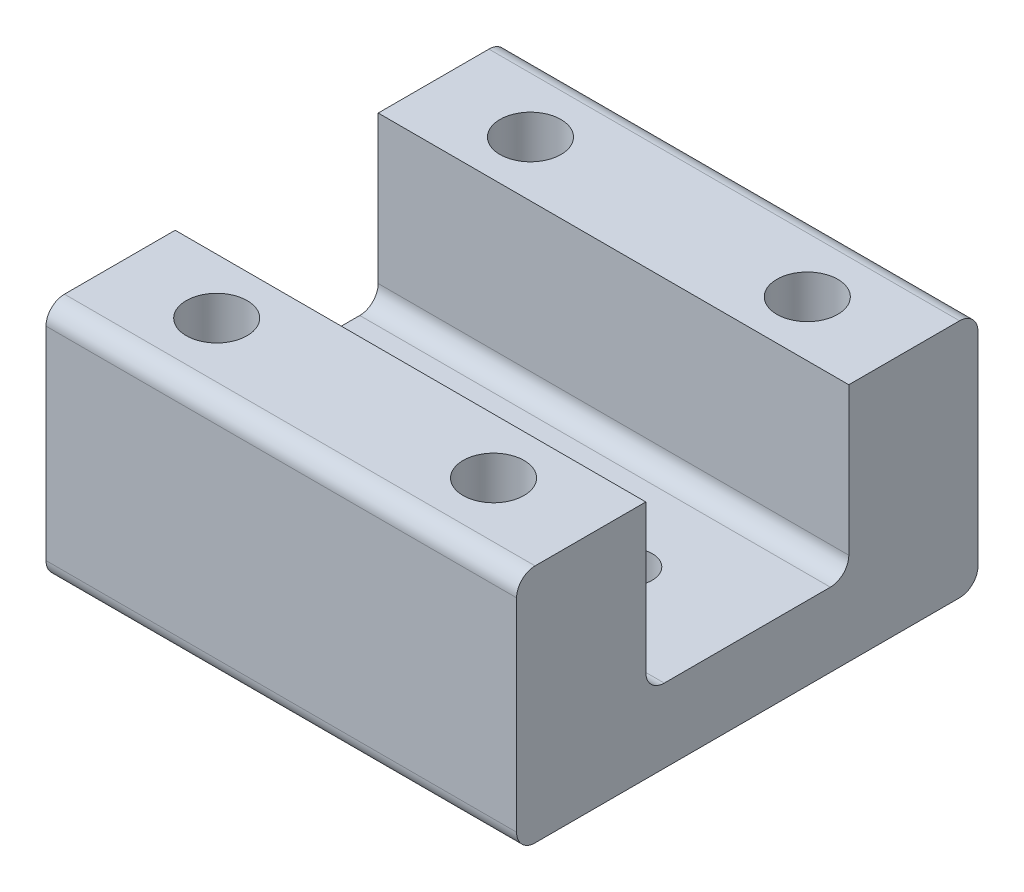
SolidWorks part; units mm, degrees
material "6063-T5"
ref_plane "前视基准面" through (0, 0, 0) normal (0, 0, 1) x (1, 0, 0)
ref_plane "上视基准面" through (0, 0, 0) normal (0, 1, 0) x (1, 0, 0)
ref_plane "右视基准面" through (0, 0, 0) normal (1, 0, 0) x (0, 0, -1)
other "Configuration Table"
sketch "草图1" plane through (0, 0, 0) normal (0, 1, 0) x (1, 0, 0)
  line L1 (-12.75, -12.5) -> (12.75, -12.5)
  line L2 (-12.75, -12.5) -> (-12.75, 12.5)
  line L3 (-12.75, 12.5) -> (12.75, 12.5)
  line L4 (12.75, -12.5) -> (12.75, 12.5)
  line L5 (-12.75, -12.5) -> (12.75, 12.5) construction
  line L6 (-12.75, 12.5) -> (12.75, -12.5) construction
  point P0 (0, 0)
  dimension "D1" = 25.5
  dimension "D2" = 25
extrude "凸台-拉伸1" add sketch "草图1" along normal blind 4
sketch "草图2" plane through (0, 0, 0) normal (0, -1, 0) x (1, 0, 0)
  line L1 (-7.5, 7.5) -> (7.5, 7.5) construction
  line L2 (-7.5, 7.5) -> (-7.5, -7.5) construction
  line L3 (-7.5, -7.5) -> (7.5, -7.5) construction
  line L4 (7.5, 7.5) -> (7.5, -7.5) construction
  line L5 (-7.5, 7.5) -> (7.5, -7.5) construction
  line L6 (-7.5, -7.5) -> (7.5, 7.5) construction
  point P0 (0, 0)
  dimension "D1" = 15
sketch "草图5" plane through (0, 0, 0) normal (0, -1, 0) x (1, 0, 0)
  line L0 (0, 0) -> (50000, 0) construction
  line L1 (12.75, 12.5) -> (12.75, -12.5) construction
  circle A0 centre (6.35, 0) radius 1.525
  circle A1 centre (-6.35, 0) radius 1.525
  dimension "D2" = 3.05
  dimension "D3" = 6.4
  dimension "D1" = 12.7
sketch "草图6" plane through (0, 4, 0) normal (0, 1, 0) x (1, 0, 0)
  line L0 (-12.75, 12.5) -> (-12.75, -12.5) construction
  line L1 (12.75, 12.5) -> (-12.75, 12.5)
  line L2 (12.75, 12.5) -> (12.75, 5.5)
  line L3 (12.75, 5.5) -> (-12.75, 5.5)
  line L4 (-12.75, 12.5) -> (-12.75, 5.5)
  line L5 (0, 0) -> (12.75, 0) construction
  line L6 (12.75, -12.5) -> (-12.75, -12.5)
  line L7 (12.75, -12.5) -> (12.75, -5.5)
  line L8 (12.75, -5.5) -> (-12.75, -5.5)
  line L9 (-12.75, -12.5) -> (-12.75, -5.5)
  line L10 (12.75, -12.5) -> (12.75, 12.5) construction
  dimension "D1" = 7
extrude "凸台-拉伸2" add sketch "草图6" along normal blind 9
sketch "草图7" plane through (0, 0, 0) normal (0, -1, 0) x (1, 0, 0)
  line L0 (-12.75, -12.5) -> (-12.75, 12.5) construction
  line L1 (-7.5, 8.5) -> (7.5, 8.5) construction
  line L2 (-7.5, 8.5) -> (-7.5, -8.5) construction
  line L3 (-7.5, -8.5) -> (7.5, -8.5) construction
  line L4 (7.5, 8.5) -> (7.5, -8.5) construction
  circle A0 centre (7.5, -8.5) radius 2.025
  circle A1 centre (-7.5, 8.5) radius 2.025
  circle A2 centre (7.5, 8.5) radius 2.025
  circle A3 centre (-7.5, -8.5) radius 2.025
  dimension "D1" = 4.05
  dimension "D2" = 15
  dimension "D3" = 8.5
  dimension "D4" = 5.25
  dimension "D5" = 8.5
hole_wizard "M3 螺纹孔1" positions "3D草图3" profile "草图10" tap size "M3" standard "GB" end condition through all
sketch3d "3D草图3"
  point P0 (6.35, 0, 0)
  point P3 (-6.35, 0, 0)
sketch "草图10" plane through (6.35, 0, 0) normal (1, 0, 0) x (0, 0, -1)
  line L0 (0, 0) -> (0, 13)
  line L1 (0, 13) -> (1.25, 13)
  line L2 (1.25, 13) -> (1.25, 0)
  line L5 (1.25, 0) -> (0, 0)
  line L11 (0, -6.35) -> (0, 107.95) construction
  dimension "通孔螺纹孔钻头直径" = 2.5
  dimension "通孔螺纹孔钻头深度" = 13
cosmetic thread "孔螺蚊线5" parameters "D2"=3
cosmetic thread "孔螺蚊线6" parameters "D2"=3
hole_wizard "M4 螺纹孔3" positions "3D草图6" profile "草图12" tap size "M4" standard "GB" end condition through all
sketch3d "3D草图6"
  point P0 (7.5, 0, 8.5)
  point P3 (-7.5, 0, 8.5)
  point P6 (-7.5, 0, -8.5)
  point P9 (7.5, 0, -8.5)
cosmetic thread "孔螺蚊线7" parameters "D2"=4
cosmetic thread "孔螺蚊线8" parameters "D2"=4
cosmetic thread "孔螺蚊线9" parameters "D2"=4
cosmetic thread "孔螺蚊线10" parameters "D2"=4
sketch "草图12" plane through (7.5, 0, 8.5) normal (1, 0, 0) x (0, 0, -1)
  line L0 (0, 0) -> (0, 13)
  line L1 (0, 13) -> (1.65, 13)
  line L2 (1.65, 13) -> (1.65, 0)
  line L5 (1.65, 0) -> (0, 0)
  line L11 (0, -6.35) -> (0, 107.95) construction
  dimension "通孔螺纹孔钻头直径" = 3.3
  dimension "通孔螺纹孔钻头深度" = 13
fillet "圆角1" radius 1 6 edges at (0, 0, -12.5) (0, 13, -12.5) (0, 4, -5.5) (0, 4, 5.5) (0, 13, 12.5) (0, 0, 12.5)
